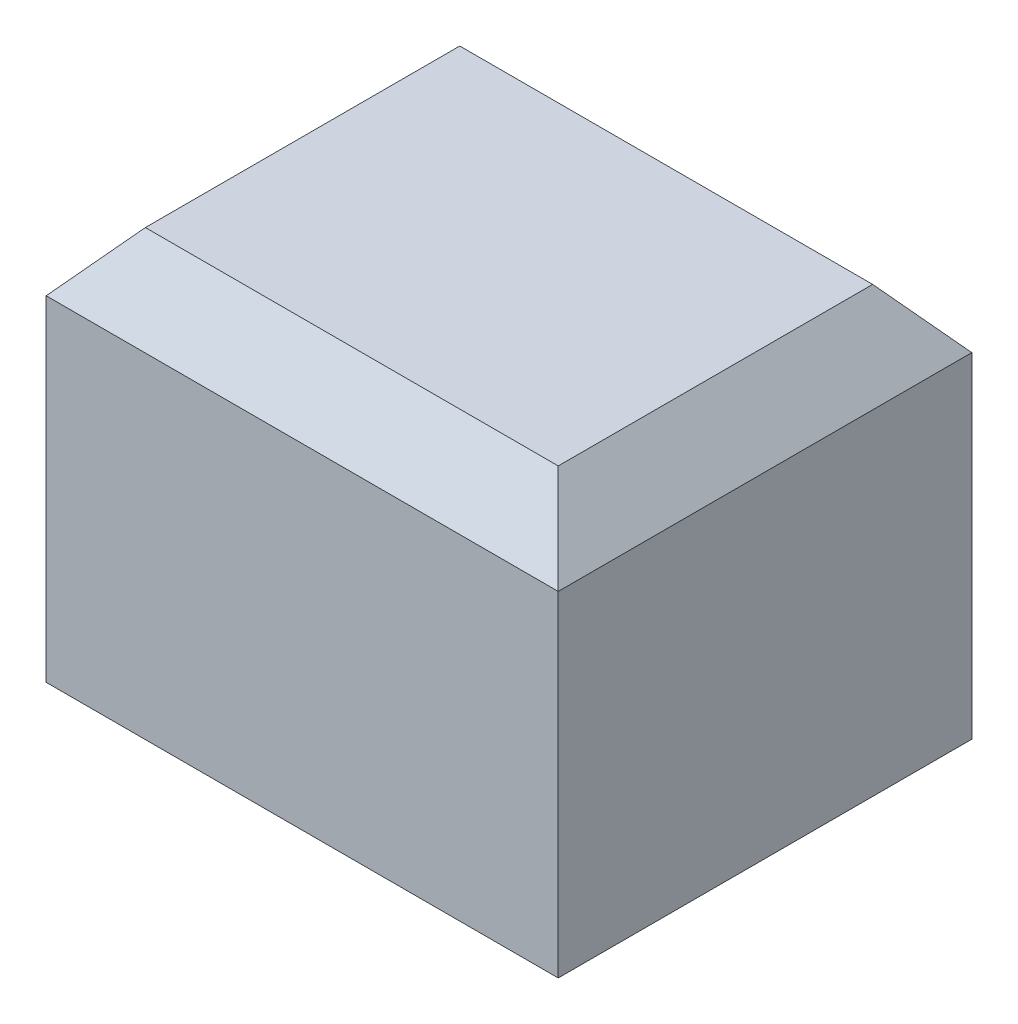
SolidWorks part; units mm, degrees
ref_plane "Front Plane" through (0, 0, 0) normal (0, 0, 1) x (1, 0, 0)
ref_plane "Top Plane" through (0, 0, 0) normal (0, 1, 0) x (1, 0, 0)
ref_plane "Right Plane" through (0, 0, 0) normal (1, 0, 0) x (0, 0, -1)
sketch "Sketch1" plane through (0, 0, 0) normal (0, 1, 0) x (1, 0, 0)
  line L0 (-2.6, -2.1) -> (2.6, -2.1)
  line L1 (-1.5, -1) -> (1.5, -1) construction
  line L2 (-1.5, -1) -> (-1.5, 1) construction
  line L3 (-1.5, 1) -> (1.5, 1) construction
  line L4 (1.5, -1) -> (1.5, 1) construction
  line L5 (-1.5, -1) -> (1.5, 1) construction
  line L6 (-1.5, 1) -> (1.5, -1) construction
  line L7 (2.6, -2.1) -> (2.6, 2.1)
  line L8 (-2.6, 2.1) -> (2.6, 2.1)
  line L9 (-2.6, -2.1) -> (-2.6, 2.1)
  line L15 (-1.5, -1) -> (1.5, -1)
  line L16 (-1.5, -1) -> (-1.5, 1)
  line L17 (-1.5, 1) -> (1.5, 1)
  line L18 (1.5, -1) -> (1.5, 1)
  point P0 (0, 0)
  dimension "D1" = 3
  dimension "D2" = 2
  dimension "D5" = 5.2
  dimension "D6" = 4.2
  dimension "D3" = 1.1
extrude "Body Extrude" add sketch "Sketch1" along normal blind 2.8
sketch "Sketch2" plane through (0, 2.8, 0) normal (0, 1, 0) x (1, 0, 0)
  line L1 (-2.6, -2.1) -> (2.6, -2.1)
  line L2 (-2.6, -2.1) -> (-2.6, 2.1)
  line L3 (-2.6, 2.1) -> (2.6, 2.1)
  line L4 (2.6, -2.1) -> (2.6, 2.1)
extrude "Cap Extrude" add sketch "Sketch2" along normal blind 1.2
chamfer "Bed Chamfer" distance 0.6 angle 40 4 edges at (0, 4, -2.1) (2.6, 4, 0) (0, 4, 2.1) (-2.6, 4, 0)
